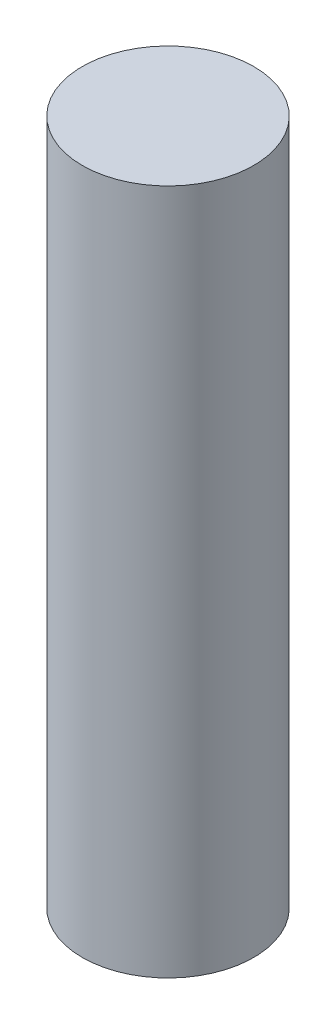
SolidWorks part; units mm, degrees
ref_plane "Front Plane" through (0, 0, 0) normal (0, 0, 1) x (1, 0, 0)
ref_plane "Top Plane" through (0, 0, 0) normal (0, 1, 0) x (1, 0, 0)
ref_plane "Right Plane" through (0, 0, 0) normal (1, 0, 0) x (0, 0, -1)
sketch "Sketch1" plane through (0, 0, 0) normal (0, 0, 1) x (1, 0, 0)
  line L0 (0, 0) -> (0, 12)
  line L4 (-1.5, 12) -> (-1.5, 0)
  line L8 (-1.5, 12) -> (0, 12)
  line L11 (-1.5, 0) -> (0, 0)
  point P0 (0, 0)
  point P11 (0, 1)
  dimension "D1" = 12
  dimension "D5" = 1.5
revolve "Revolve1" add sketch "Sketch1" angle 360 about L0
